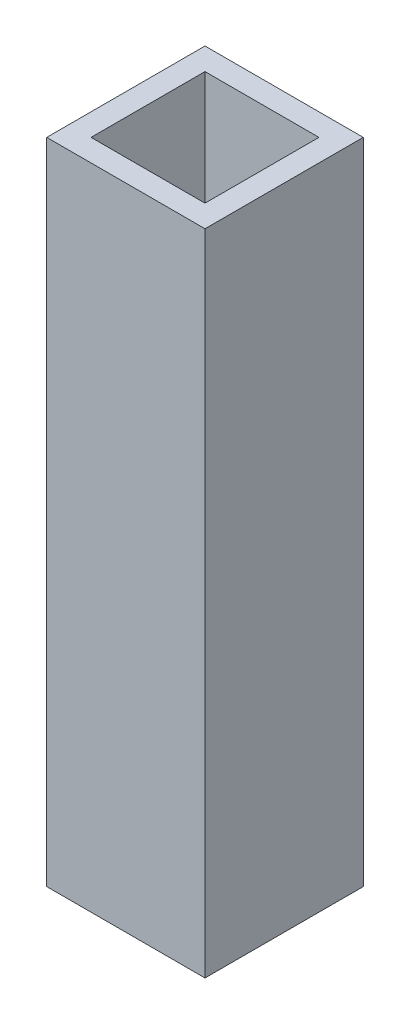
SolidWorks part; units mm, degrees
material "6061 Alloy"
ref_plane "Front Plane" through (0, 0, 0) normal (0, 0, 1) x (1, 0, 0)
ref_plane "Top Plane" through (0, 0, 0) normal (0, 1, 0) x (1, 0, 0)
ref_plane "Right Plane" through (0, 0, 0) normal (1, 0, 0) x (0, 0, -1)
sketch "Sketch1" plane through (0, 0, 0) normal (0, 1, 0) x (1, 0, 0)
  line L0 (-18, 18) -> (18, 18)
  line L1 (-25, 25) -> (25, 25)
  line L2 (-25, 25) -> (-25, -25)
  line L3 (-25, -25) -> (25, -25)
  line L4 (25, 25) -> (25, -25)
  line L5 (-25, 25) -> (25, -25) construction
  line L6 (-25, -25) -> (25, 25) construction
  line L7 (18, 18) -> (18, -18)
  line L8 (-18, -18) -> (18, -18)
  line L9 (-18, 18) -> (-18, -18)
  point P0 (0, 0)
  dimension "D1" = 50
  dimension "D2" = 50
  dimension "D3" = 7
extrude "Boss-Extrude1" add sketch "Sketch1" along normal blind 205
